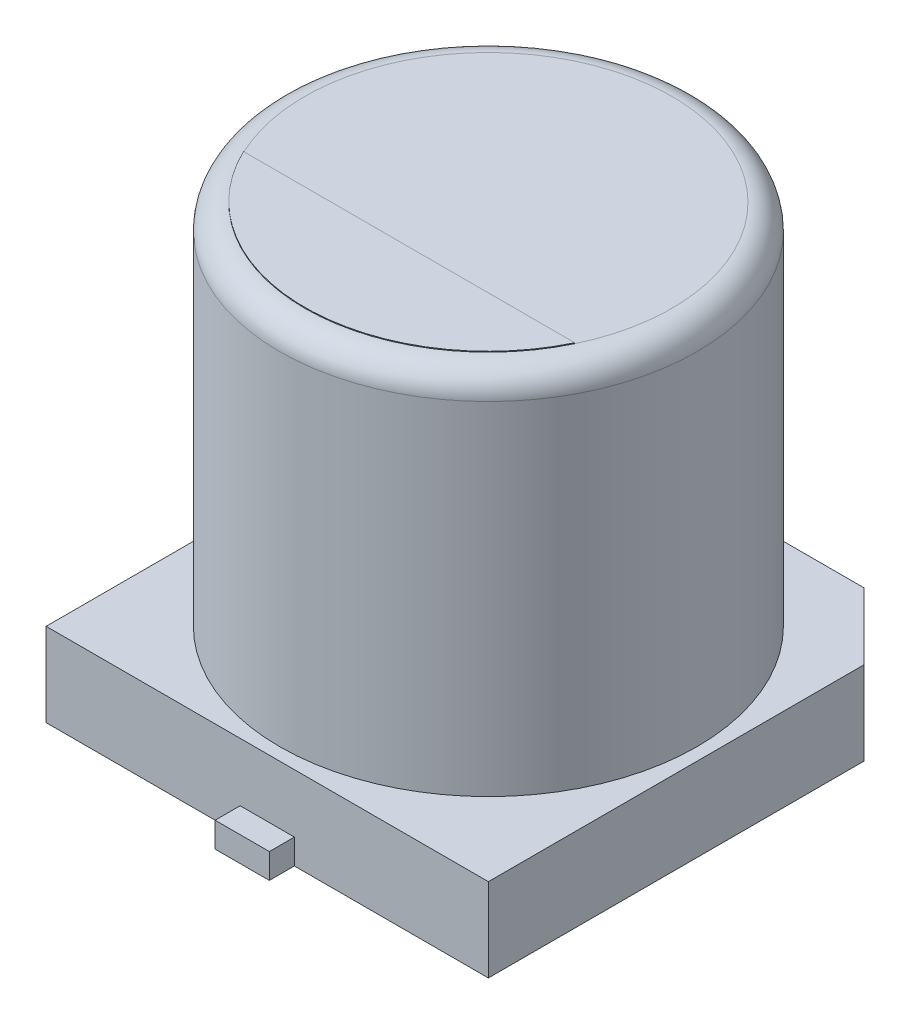
SolidWorks part; units mm, degrees
ref_plane "Front Plane" through (0, 0, 0) normal (0, 0, 1) x (1, 0, 0)
ref_plane "Top Plane" through (0, 0, 0) normal (0, 1, 0) x (1, 0, 0)
ref_plane "Right Plane" through (0, 0, 0) normal (1, 0, 0) x (0, 0, -1)
sketch "Sketch2" plane through (0, 0, 0) normal (0, 1, 0) x (1, 0, 0)
  line L0 (0, 0) -> (0, 2.085) construction
  line L1 (0, 0) -> (2.9643, 0) construction
  line L2 (2.65, -2.65) -> (-2.65, -2.65)
  line L3 (-2.65, -2.65) -> (-2.65, 1.85)
  line L4 (-2.65, 1.85) -> (-1.85, 2.65)
  line L5 (-1.85, 2.65) -> (1.85, 2.65)
  line L6 (1.85, 2.65) -> (2.65, 1.85)
  line L7 (2.65, 1.85) -> (2.65, -2.65)
  line L8 (0, -2.65) -> (0, -0.9795) construction
  line L9 (0, 2.65) -> (0, 2.1922) construction
  line L10 (-0.2934, -2.65) -> (-0.2934, 2.65) construction
  line L11 (-0.2934, 0) -> (-0.8682, 0) construction
  dimension "D1" = 5.3
  dimension "D2" = 5.3
  dimension "D3" = 3.7
extrude "Boss-Extrude1" add sketch "Sketch2" along normal blind 1
sketch "Sketch3" plane through (0, 0, 0) normal (0, 1, 0) x (1, 0, 0)
  circle A0 centre (0, 0) radius 2.5
  dimension "D1" = 5
extrude "Boss-Extrude2" add sketch "Sketch3" along normal blind 5.4 contours A0
fillet "Fillet1" radius 0.3 1 edges at (0, 5.4, 2.5)
sketch "Sketch4" plane through (0, 0, 0) normal (0, 1, 0) x (1, 0, 0)
  line L0 (0, 0) -> (1.5414, 0) construction
  line L1 (0.325, 2.95) -> (-0.325, 2.95)
  line L2 (0.325, -0.75) -> (-0.325, -0.75)
  line L3 (0.325, -0.75) -> (0.325, -2.95)
  line L4 (0.325, -2.95) -> (-0.325, -2.95)
  line L5 (-0.325, -0.75) -> (-0.325, -2.95)
  line L6 (0.325, -0.75) -> (-0.325, -2.95) construction
  line L7 (0.325, -2.95) -> (-0.325, -0.75) construction
  line L8 (-0.325, 0.75) -> (-0.325, 2.95)
  line L9 (0.325, 0.75) -> (-0.325, 0.75)
  line L10 (0.325, 0.75) -> (0.325, 2.95)
  line L11 (0.325, 2.95) -> (-0.325, 0.75) construction
  line L12 (0.325, 0.75) -> (-0.325, 2.95) construction
  point P1 (0, -1.85)
  point P12 (0, 1.85)
  dimension "D1" = 0.65
  dimension "D2" = 2.2
  dimension "D3" = 1.5
extrude "Boss-Extrude3" add sketch "Sketch4" along normal blind 0.3
ref_plane "Plane1" through (0, 5.4, 0) normal (0, 1, 0) x (1, 0, 0)
sketch "Sketch5" plane through (0, 5.4, 0) normal (0, 1, 0) x (1, 0, 0)
  line L0 (-1.9845, -0.9496) -> (1.9845, -0.9496)
  circle A0 centre (0, 0) radius 2.2 construction
  arc A1 (-1.9845, -0.9496) -> (1.9845, -0.9496) centre (0, 0) ccw
extrude "Boss-Extrude4" add sketch "Sketch5" along normal blind 0.01
